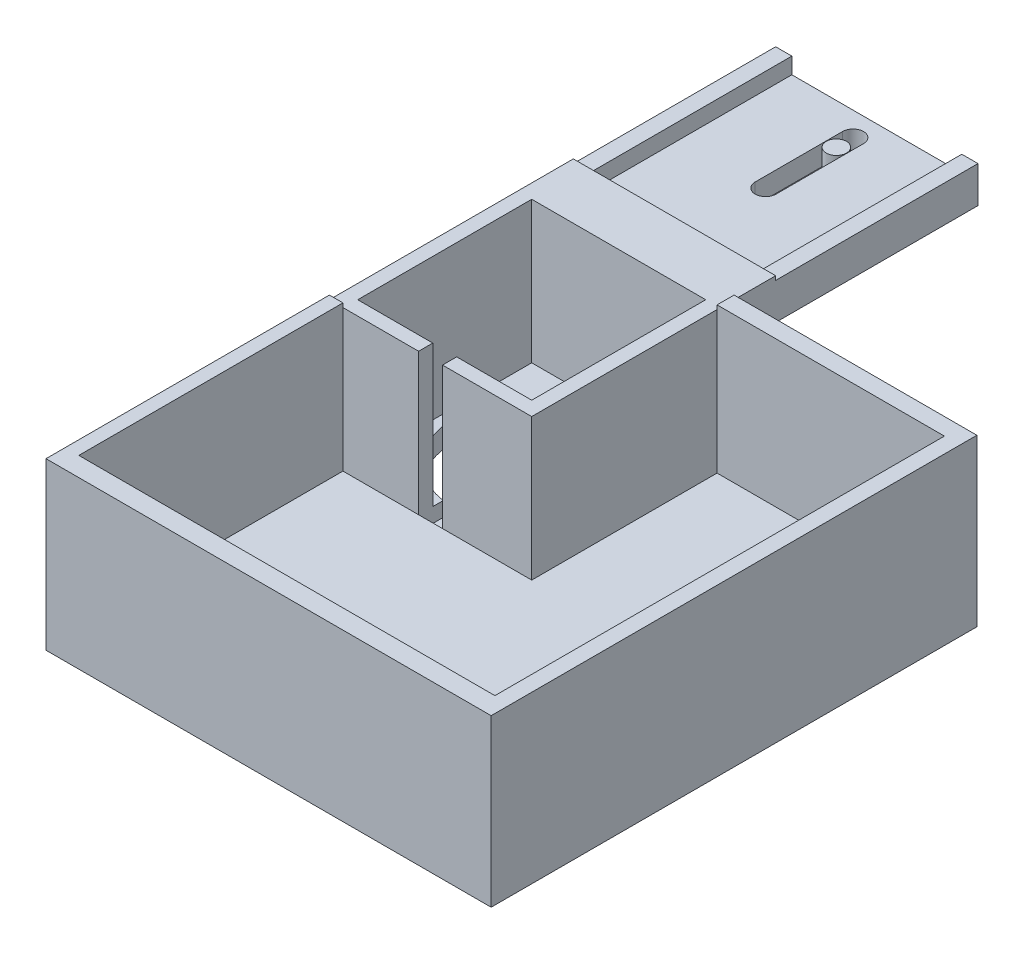
SolidWorks part; units mm, degrees
ref_plane "Alzado" through (0, 0, 0) normal (0, 0, 1) x (1, 0, 0)
ref_plane "Planta" through (0, 0, 0) normal (0, 1, 0) x (1, 0, 0)
ref_plane "Vista lateral" through (0, 0, 0) normal (1, 0, 0) x (0, 0, -1)
sketch "Croquis1" plane through (0, 0, 0) normal (0, 1, 0) x (1, 0, 0)
  line L1 (-25, -25) -> (25, -25)
  line L2 (-25, -25) -> (-25, 25)
  line L3 (-25, 25) -> (25, 25)
  line L4 (25, -25) -> (25, 25)
  line L5 (-25, -25) -> (25, 25) construction
  line L6 (-25, 25) -> (25, -25) construction
  point P0 (0, 0)
  dimension "D1" = 50
  dimension "D2" = 50
extrude "Saliente-Extruir1" add sketch "Croquis1" along normal blind 40
sketch "Croquis3" plane through (0, 40, 0) normal (0, 1, 0) x (1, 0, 0)
  line L1 (-21.5, -21.5) -> (21.5, -21.5)
  line L2 (-21.5, -21.5) -> (-21.5, 21.5)
  line L3 (-21.5, 21.5) -> (21.5, 21.5)
  line L4 (21.5, -21.5) -> (21.5, 21.5)
  line L5 (-21.5, -21.5) -> (21.5, 21.5) construction
  line L6 (-21.5, 21.5) -> (21.5, -21.5) construction
  point P0 (0, 0)
  dimension "D1" = 43
  dimension "D2" = 43
extrude "Cortar-Extruir3" cut sketch "Croquis3" against normal blind 35
sketch "Croquis4" plane through (25, 0, 0) normal (1, 0, 0) x (0, 0, -1)
  line L0 (-25, 25.1629) -> (-11.3423, 40)
  line L1 (-25, 40) -> (-25, 0) construction
  line L2 (-25, 40) -> (25, 40) construction
  line L3 (-11.3423, 40) -> (-25, 40)
  line L4 (-25, 40) -> (-25, 25.4839)
sketch "Croquis5" plane through (0, 0, 0) normal (1, 0, 0) x (0, 0, -1)
  line L1 (25, 40) -> (35.2791, 40)
  line L2 (25, 40) -> (25, 30)
  line L3 (25, 30) -> (35.2791, 30)
  line L4 (35.2791, 40) -> (35.2791, 30)
  dimension "D1" = 10.2791
  dimension "D2" = 10
extrude "Saliente-Extruir2" add sketch "Croquis5" along normal blind 25 and the other way blind 25
sketch "Croquis6" plane through (0, 0, 0) normal (1, 0, 0) x (0, 0, -1)
  line L1 (35.2791, 30) -> (85.2791, 30)
  line L2 (35.2791, 30) -> (35.2791, 35)
  line L3 (35.2791, 35) -> (85.2791, 35)
  line L4 (85.2791, 30) -> (85.2791, 35)
  dimension "D1" = 5
  dimension "D2" = 50
extrude "Saliente-Extruir3" add sketch "Croquis6" along normal blind 25 and the other way blind 25
sketch "Croquis7" plane through (0, 35, 0) normal (0, 1, 0) x (1, 0, 0)
  line L0 (-25, 35.2791) -> (25, 35.2791) construction
  line L1 (25, 85.2791) -> (21, 85.2791)
  line L2 (25, 85.2791) -> (25, 35.2791)
  line L3 (25, 35.2791) -> (21, 35.2791)
  line L4 (21, 85.2791) -> (21, 35.2791)
  line L5 (0, 64.8964) -> (0, 32.4772) construction
  line L6 (-25, 35.2791) -> (-21, 35.2791)
  line L7 (-25, 85.2791) -> (-25, 35.2791)
  line L8 (-25, 85.2791) -> (-21, 85.2791)
  line L9 (-21, 85.2791) -> (-21, 35.2791)
  dimension "D1" = 4
extrude "Saliente-Extruir4" add sketch "Croquis7" along normal blind 4
sketch "Croquis8" plane through (0, 35, 0) normal (0, 1, 0) x (1, 0, 0)
  line L0 (-21, 85.2791) -> (21, 85.2791) construction
  line L1 (0, 79.4068) -> (0, 57.8001) construction
  line L2 (2.5948, 79.4068) -> (2.5948, 57.8001)
  line L3 (-2.5948, 79.4068) -> (-2.5948, 57.8001)
  circle A0 centre (0, 75.2791) radius 2.5
  arc A1 (2.5948, 79.4068) -> (-2.5948, 79.4068) centre (0, 79.4068) ccw
  arc A2 (-2.5948, 57.8001) -> (2.5948, 57.8001) centre (0, 57.8001) ccw
  point P7 (0, 68.6034)
  dimension "D2" = 5
  dimension "D1" = 10
extrude "Cortar-Extruir5" cut sketch "Croquis8" against normal blind 24 and the other way blind 4
sketch "Croquis12" plane through (0, 0, 25) normal (0, 0, 1) x (1, 0, 0)
  line L0 (0, 0) -> (0, 49.0863) construction
  line L1 (-25, 0) -> (25, 0) construction
  line L3 (-2.9557, 1.387) -> (2.9557, 1.387)
  line L4 (-2.9557, 1.387) -> (-2.9557, 40.4074)
  line L5 (-2.9557, 40.4074) -> (2.9557, 40.4074)
  line L6 (2.9557, 1.387) -> (2.9557, 40.4074)
  line L7 (-2.9557, 1.387) -> (2.9557, 40.4074) construction
  line L8 (-2.9557, 40.4074) -> (2.9557, 1.387) construction
  point P4 (0, 20.8972)
extrude "Cortar-Extruir7" cut sketch "Croquis12" against normal blind 10
sketch "Croquis13" plane through (0, 0, 0) normal (0, -1, 0) x (1, 0, 0)
  circle A0 centre (0, 0) radius 19.1447
extrude "Cortar-Extruir8" cut sketch "Croquis13" against normal blind 10
sketch "Croquis14" plane through (0, 0, 0) normal (0, 1, 0) x (1, 0, 0)
  line L2 (25, -25) -> (25, 25)
  line L3 (25, 25) -> (85, 25)
  line L4 (85, -25) -> (85, 25)
  line L5 (-25, -25) -> (25, -25)
  line L6 (-25, -25) -> (-25, -95.0287)
  line L7 (-25, -95.0287) -> (85, -95.0287)
  line L8 (85, -25) -> (85, -95.0287)
  dimension "D1" = 50
  dimension "D2" = 60
extrude "Saliente-Extruir6" add sketch "Croquis14" along normal blind 41
sketch "Croquis15" plane through (0, 41, 0) normal (0, 1, 0) x (1, 0, 0)
  line L0 (25, 20.7999) -> (81.1747, 20.7999)
  line L1 (25, 25) -> (25, -25) construction
  line L2 (81.1747, 20.7999) -> (81.1747, -90.2738)
  line L3 (81.1747, -90.2738) -> (-21.6469, -90.2738)
  line L4 (-21.6469, -90.2738) -> (-21.6469, -25)
  line L5 (25, -25) -> (-25, -25) construction
  line L6 (-21.6469, -25) -> (-2.9557, -25)
  line L7 (-21.6469, -25) -> (25, -25)
  line L9 (2.9557, -18.9151) -> (2.9557, -25) construction
  line L10 (2.9557, -21.9576) -> (2.9557, -25)
  line L11 (2.9557, -25) -> (25, -25)
  line L12 (25, -25) -> (25, 20.7999)
  line L13 (25, -25) -> (25.1225, -25.1924)
extrude "Cortar-Extruir9" cut sketch "Croquis15" against normal blind 36
sketch "Croquis16" plane through (-25, 0, 0) normal (-1, 0, 0) x (0, 0, 1)
  line L1 (89.864, 5.6146) -> (80.664, 5.6146)
  line L2 (89.864, 5.6146) -> (89.864, 17.6146)
  line L3 (89.864, 17.6146) -> (80.664, 17.6146)
  line L4 (80.664, 5.6146) -> (80.664, 17.6146)
  dimension "D1" = 9.2
  dimension "D2" = 12
extrude "Cortar-Extruir10" cut sketch "Croquis16" against normal blind 36
